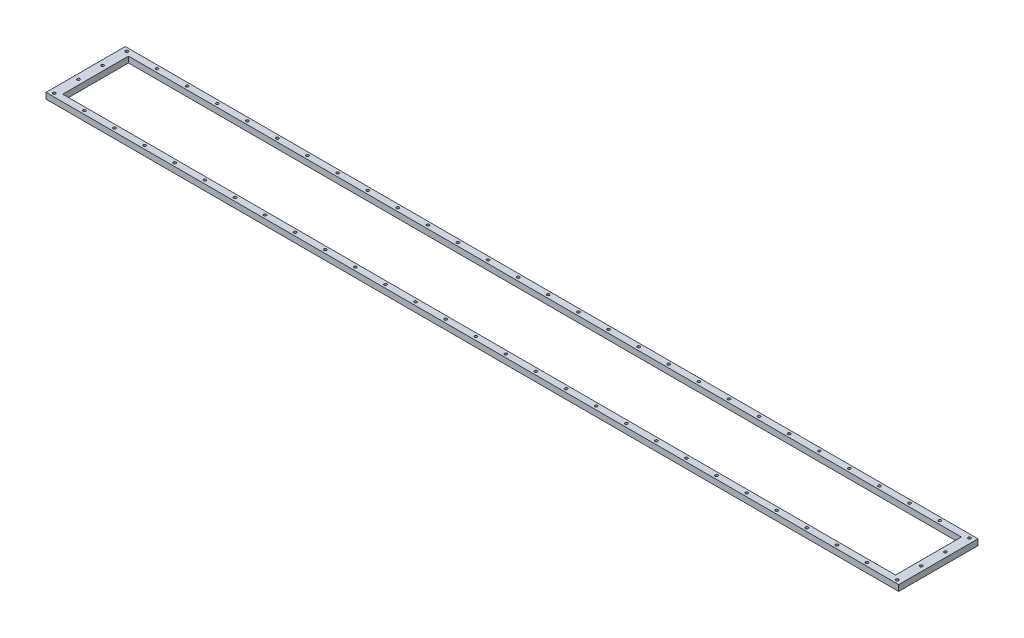
SolidWorks part; units mm, degrees
ref_plane "Front Plane" through (0, 0, 0) normal (0, 0, 1) x (1, 0, 0)
ref_plane "Top Plane" through (0, 0, 0) normal (0, 1, 0) x (1, 0, 0)
ref_plane "Right Plane" through (0, 0, 0) normal (1, 0, 0) x (0, 0, -1)
sketch "Sketch2" plane through (0, 0, 0) normal (0, 1, 0) x (1, 0, 0)
  line L1 (-537.5, -50) -> (537.5, -50)
  line L2 (-537.5, -50) -> (-537.5, 50)
  line L3 (-537.5, 50) -> (537.5, 50)
  line L4 (537.5, -50) -> (537.5, 50)
  line L5 (-537.5, -50) -> (537.5, 50) construction
  line L6 (-537.5, 50) -> (537.5, -50) construction
  line L7 (525, -41.5) -> (-525, -41.5)
  line L8 (525, -41.5) -> (525, 41.5)
  line L9 (525, 41.5) -> (-525, 41.5)
  line L10 (-525, -41.5) -> (-525, 41.5)
  line L11 (525, -41.5) -> (-525, 41.5) construction
  line L12 (525, 41.5) -> (-525, -41.5) construction
  point P0 (0, 0)
  point P6 (0, 0)
  dimension "D1" = 1075
  dimension "D2" = 100
  dimension "D3" = 1050
  dimension "D4" = 83
extrude "Boss-Extrude1" add sketch "Sketch2" along normal blind 7.5
sketch "Sketch3" plane through (0, 0, 0) normal (0, -1, 0) x (1, 0, 0)
  line L0 (-525, 41.5) -> (-525, 50) construction
  line L1 (-537.5, 50) -> (537.5, 50) construction
  line L2 (-525, 50) -> (-525, 45.75) construction
  line L3 (-525, 45.75) -> (-537.5, 45.75) construction
  line L4 (-537.5, -50) -> (-537.5, 50) construction
  line L5 (-537.5, 45.75) -> (-531.25, 45.75) construction
  circle A0 centre (-531.25, 45.75) radius 1.7
extrude "Cut-Extrude1" cut sketch "Sketch3" against normal through all both and the other way through all
pattern_linear "LPattern1" count 4 spacing 30.425 along (0, 0, -1) of "Cut-Extrude1"
pattern_linear "LPattern2" count 29 spacing 37.95 along (1, 0, 0) of "Cut-Extrude1"
ref_plane "Plane1" through (0, 0, 0) normal (0, 0, 1) x (1, 0, 0)
ref_plane "Plane2" through (0, 0, 0) normal (1, 0, 0) x (0, 0, -1)
mirror "Mirror1" about plane through (0, 0, 0) normal (0, 0, 1) of "LPattern2", "Cut-Extrude1"
mirror "Mirror2" about plane through (0, 0, 0) normal (1, 0, 0) of "LPattern1", "Cut-Extrude1"
